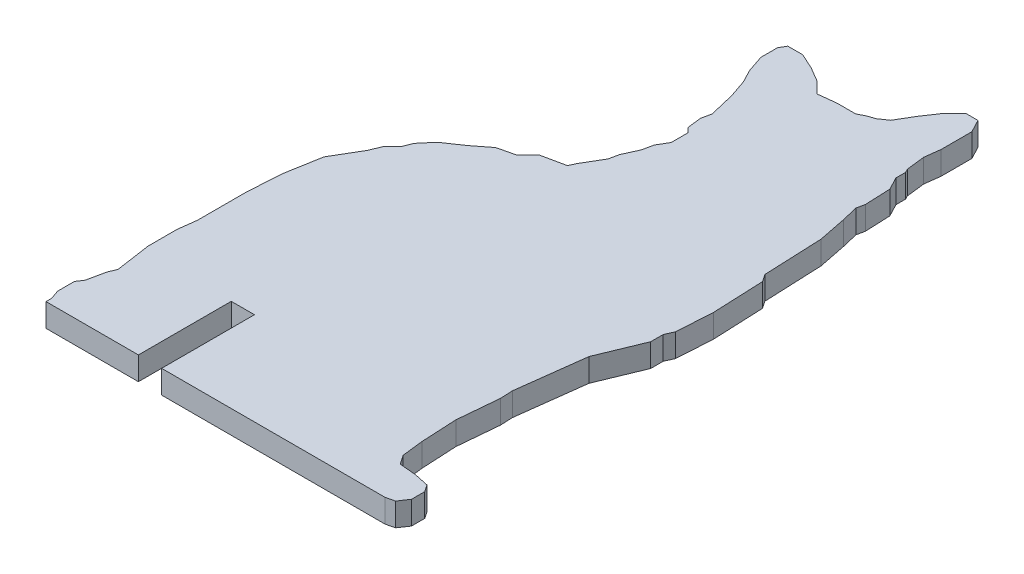
SolidWorks part; units mm, degrees
ref_plane "Front Plane" through (0, 0, 0) normal (0, 0, 1) x (1, 0, 0)
ref_plane "Top Plane" through (0, 0, 0) normal (0, 1, 0) x (1, 0, 0)
ref_plane "Right Plane" through (0, 0, 0) normal (1, 0, 0) x (0, 0, -1)
sketch "Sketch1" plane through (0, 0, 0) normal (0, 1, 0) x (1, 0, 0)
  line L0 (100, 500) -> (500, 500) construction
  line L1 (19.0213, 44.8042) -> (19.3324, 45.4887)
  line L2 (19.3324, 45.4887) -> (20.5771, 47.6047)
  line L3 (20.5771, 47.6047) -> (20.795, 48.6316)
  line L4 (20.795, 48.6316) -> (21.5271, 50.2423)
  line L5 (21.5271, 50.2423) -> (21.771, 51.3921)
  line L6 (21.771, 51.3921) -> (22.4479, 52.5429)
  line L7 (22.4479, 52.5429) -> (22.4479, 54.3573)
  line L8 (22.4479, 54.3573) -> (21.9482, 54.857)
  line L9 (21.9482, 54.857) -> (21.771, 56.3799)
  line L10 (21.771, 56.3799) -> (21.991, 57.4171)
  line L11 (21.991, 57.4171) -> (21.771, 58.3403)
  line L12 (21.771, 58.3403) -> (21.3403, 60.1476)
  line L13 (21.3403, 60.1476) -> (20.6861, 62.0744)
  line L14 (20.6861, 62.0744) -> (19.9548, 63.4747)
  line L15 (19.9548, 63.4747) -> (19.3324, 65.3077)
  line L16 (19.3324, 65.3077) -> (19.3324, 67.1155)
  line L17 (19.3324, 67.1155) -> (19.7412, 67.8104)
  line L18 (19.7412, 67.8104) -> (21.3403, 67.8104)
  line L19 (21.3403, 67.8104) -> (22.9927, 67.0593)
  line L20 (22.9927, 67.0593) -> (24.5184, 66.1619)
  line L21 (24.5184, 66.1619) -> (25.7609, 64.9193)
  line L22 (25.7609, 64.9193) -> (27.6871, 65.1434)
  line L23 (27.6871, 65.1434) -> (29.7249, 65.1434)
  line L24 (29.7249, 65.1434) -> (30.4854, 65.5406)
  line L25 (30.4854, 65.5406) -> (31.2798, 65.8103)
  line L26 (31.2798, 65.8103) -> (32.2018, 66.4377)
  line L27 (32.2018, 66.4377) -> (33.2548, 68.2278)
  line L28 (33.2548, 68.2278) -> (34.2762, 69.7428)
  line L29 (34.2762, 69.7428) -> (35.2434, 70.71)
  line L30 (35.2434, 70.71) -> (35.6563, 71.1228)
  line L31 (35.6563, 71.1228) -> (36.9132, 71.1228)
  line L32 (36.9132, 71.1228) -> (37.6339, 69.7428)
  line L33 (37.6339, 69.7428) -> (37.6339, 66.4377)
  line L34 (37.6339, 66.4377) -> (37.4231, 64.7676)
  line L35 (37.4231, 64.7676) -> (37.655, 62.7746)
  line L36 (37.655, 62.7746) -> (37.8558, 62.39)
  line L37 (37.8558, 62.39) -> (37.8558, 61.3395)
  line L38 (37.8558, 61.3395) -> (38.5709, 59.9702)
  line L39 (38.5709, 59.9702) -> (38.6888, 57.2258)
  line L40 (38.6888, 57.2258) -> (38.5094, 56.3799)
  line L41 (38.5094, 56.3799) -> (38.9319, 54.6072)
  line L42 (38.9319, 54.6072) -> (39.5327, 51.6002)
  line L43 (39.5327, 51.6002) -> (39.6602, 48.6316)
  line L44 (39.6602, 48.6316) -> (39.8046, 45.2718)
  line L45 (39.8046, 45.2718) -> (40.3394, 44.4858)
  line L46 (40.3394, 44.4858) -> (40.577, 38.9567)
  line L47 (40.577, 38.9567) -> (40.3394, 35.1141)
  line L48 (40.3394, 35.1141) -> (39.9271, 34.2069)
  line L49 (39.9271, 34.2069) -> (39.9271, 32.8599)
  line L50 (39.9271, 32.8599) -> (37.9856, 28.1485)
  line L51 (37.9856, 28.1485) -> (37.0605, 20.8212)
  line L52 (37.0605, 20.8212) -> (37.119, 19.4607)
  line L53 (37.119, 19.4607) -> (36.7199, 15.069)
  line L54 (36.7199, 15.069) -> (36.9194, 11.219)
  line L55 (36.9194, 11.219) -> (37.1855, 8.9325)
  line L56 (37.1855, 8.9325) -> (37.8558, 7.9475)
  line L57 (37.8558, 7.9475) -> (39.6602, 7.7835)
  line L58 (39.6602, 7.7835) -> (41.2327, 7.45)
  line L59 (41.2327, 7.45) -> (41.7416, 6.7023)
  line L60 (41.7416, 6.7023) -> (41.7416, 5.2769)
  line L61 (41.7416, 5.2769) -> (41.0509, 4.2526)
  line L62 (41.0509, 4.2526) -> (40.1333, 4.0339)
  line L63 (40.1333, 4.0339) -> (3.6167, 4.0339)
  line L64 (3.6167, 4.0339) -> (3.6167, 4.6265)
  line L65 (3.6167, 4.6265) -> (3.27, 5.6477)
  line L66 (3.27, 5.6477) -> (3.27, 6.2614)
  line L67 (3.27, 6.2614) -> (3.27, 7.45)
  line L68 (3.27, 7.45) -> (3.7347, 8.1393)
  line L69 (3.7347, 8.1393) -> (4.1455, 10.0757)
  line L70 (4.1455, 10.0757) -> (4.4938, 10.9209)
  line L71 (4.4938, 10.9209) -> (3.9401, 14.6998)
  line L72 (3.9401, 14.6998) -> (3.9401, 17.8115)
  line L73 (3.9401, 17.8115) -> (4.1894, 19.7858)
  line L74 (4.1894, 19.7858) -> (4.1894, 24.9715)
  line L75 (4.1894, 24.9715) -> (4.4177, 28.6647)
  line L76 (4.4177, 28.6647) -> (5.0934, 32.5083)
  line L77 (5.0934, 32.5083) -> (6.8329, 35.4654)
  line L78 (6.8329, 35.4654) -> (7.3079, 36.6182)
  line L79 (7.3079, 36.6182) -> (8.2578, 37.5681)
  line L80 (8.2578, 37.5681) -> (8.6944, 38.6274)
  line L81 (8.6944, 38.6274) -> (9.84, 39.9798)
  line L82 (9.84, 39.9798) -> (11.7865, 41.3045)
  line L83 (11.7865, 41.3045) -> (13.4615, 42.6168)
  line L84 (13.4615, 42.6168) -> (15.3485, 43.0665)
  line L85 (15.3485, 43.0665) -> (16.5548, 44.2728)
  line L86 (16.5548, 44.2728) -> (19.0213, 44.8042)
extrude "Boss-Extrude1" add sketch "Sketch1" along normal blind 2.5
sketch "Sketch2" plane through (0, 0, -4.0339) normal (0, 0, 1) x (1, 0, 0)
  line L0 (3.6167, 2.5) -> (40.1333, 2.5) construction
  line L1 (13.57, 2.5) -> (16.07, 2.5)
  line L2 (13.57, 2.5) -> (13.57, 0)
  line L3 (13.57, 0) -> (16.07, 0)
  line L4 (16.07, 2.5) -> (16.07, 0)
  line L5 (3.6167, 0) -> (40.1333, 0) construction
  line L6 (3.27, 2.5) -> (3.27, 0) construction
  dimension "D1" = 2.5
  dimension "D2" = 10.3
extrude "Cut-Extrude1" cut sketch "Sketch2" against normal blind 10
